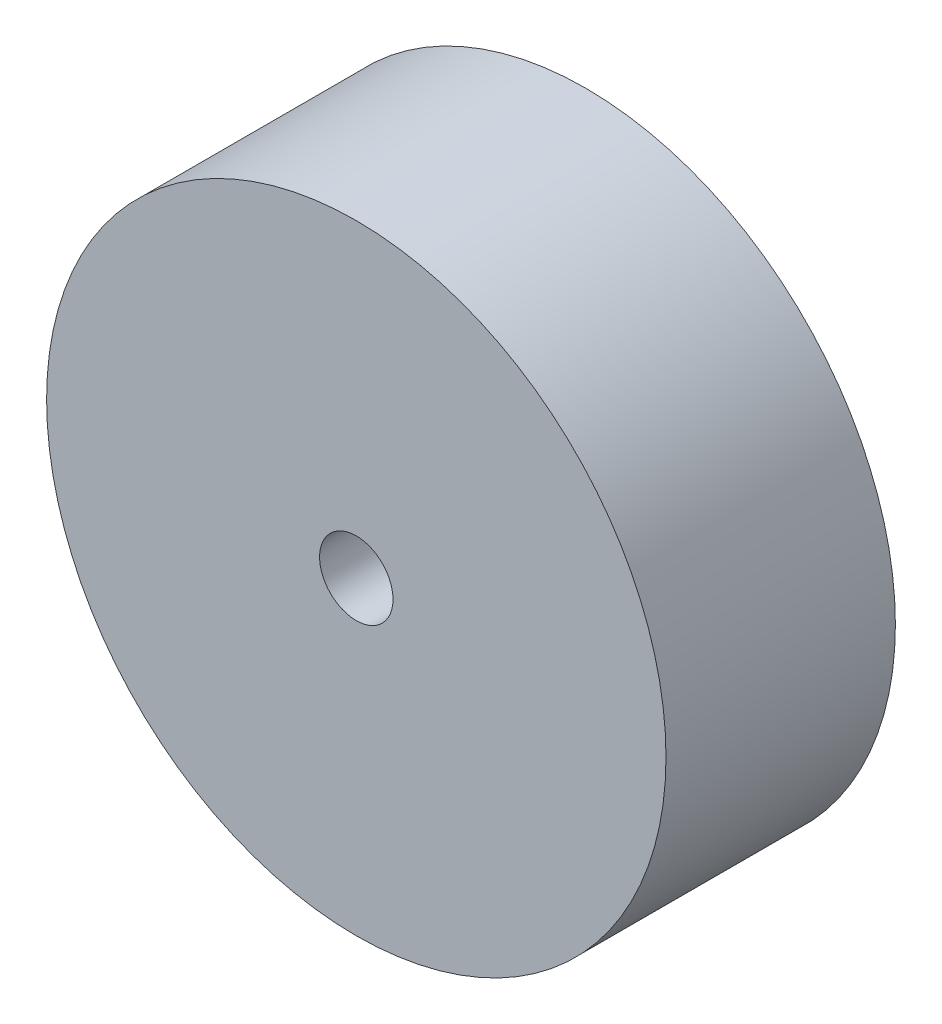
SolidWorks part; units mm, degrees
ref_plane "Front Plane" through (0, 0, 0) normal (0, 0, 1) x (1, 0, 0)
ref_plane "Top Plane" through (0, 0, 0) normal (0, 1, 0) x (1, 0, 0)
ref_plane "Right Plane" through (0, 0, 0) normal (1, 0, 0) x (0, 0, -1)
sketch "Sketch1" plane through (0, 0, 0) normal (0, 0, 1) x (1, 0, 0)
  circle A0 centre (0, 0) radius 67.5
  circle A1 centre (0, 0) radius 8
  dimension "D1" = 135
  dimension "D2" = 16
extrude "Boss-Extrude1" add sketch "Sketch1" along normal blind 50
